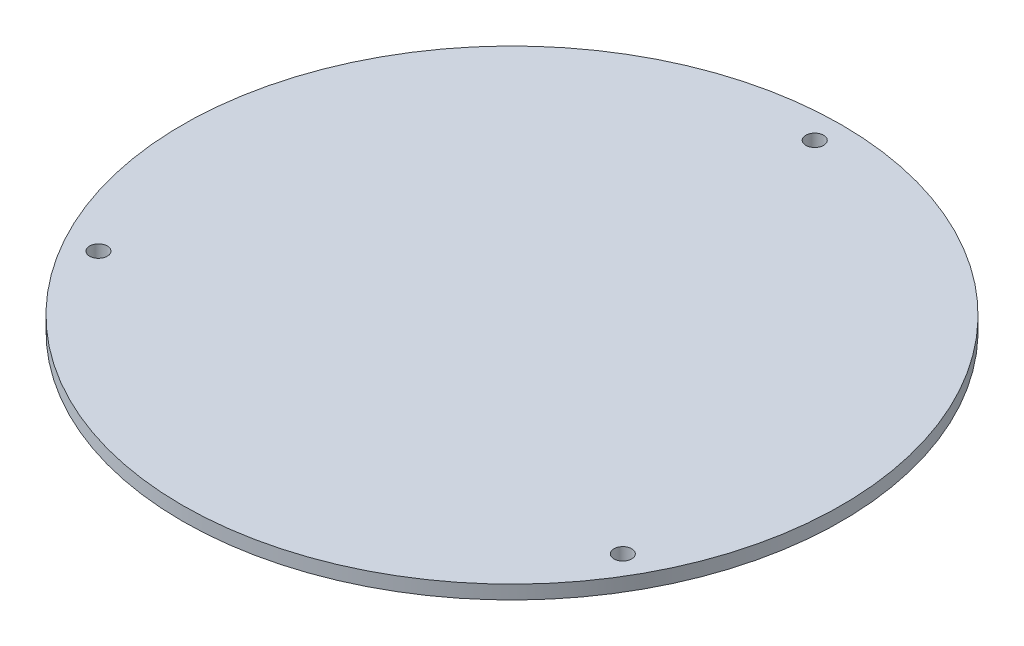
SolidWorks part; units mm, degrees
ref_plane "Front Plane" through (0, 0, 0) normal (0, 0, 1) x (1, 0, 0)
ref_plane "Top Plane" through (0, 0, 0) normal (0, 1, 0) x (1, 0, 0)
ref_plane "Right Plane" through (0, 0, 0) normal (1, 0, 0) x (0, 0, -1)
sketch "Sketch1" plane through (0, 0, 0) normal (0, 1, 0) x (1, 0, 0)
  circle A0 centre (0, 0) radius 152.4
  dimension "D1" = 304.8
extrude "Boss-Extrude1" add sketch "Sketch1" along normal blind 6.35
sketch "Sketch2" plane through (0, 6.35, 0) normal (0, 1, 0) x (1, 0, 0)
  line L0 (0, 0) -> (0, 140) construction
  circle A0 centre (0, 140) radius 4.1
  dimension "D2" = 8.2
  dimension "D1" = 140
extrude "Cut-Extrude1" cut sketch "Sketch2" against normal through all
pattern_circular "CirPattern1" count 3 every 120 about axis through (0, 0, 0) along (0, 1, 0) of "Cut-Extrude1"
